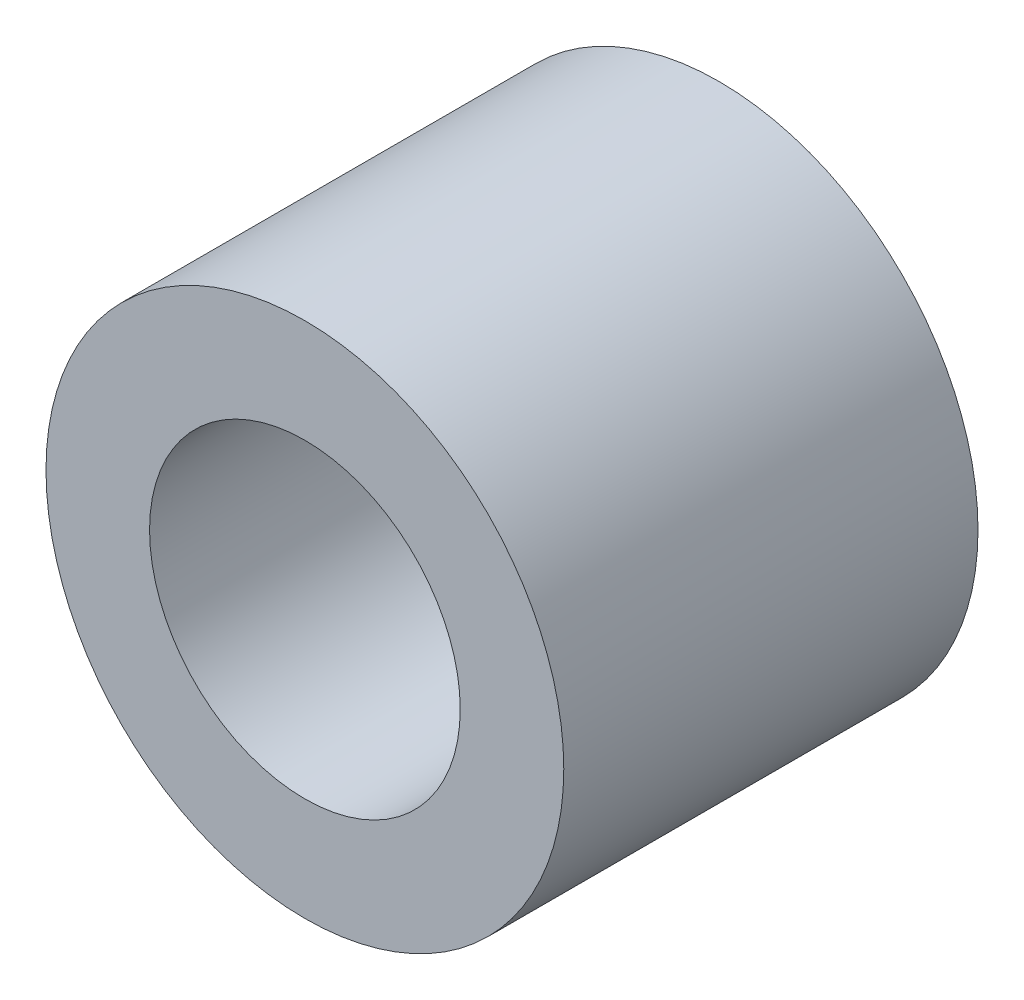
SolidWorks part; units mm, degrees
ref_plane "Płaszczyzna przednia" through (0, 0, 0) normal (0, 0, 1) x (1, 0, 0)
ref_plane "Płaszczyzna górna" through (0, 0, 0) normal (0, 1, 0) x (1, 0, 0)
ref_plane "Płaszczyzna prawa" through (0, 0, 0) normal (1, 0, 0) x (0, 0, -1)
sketch "Sketch1" plane through (0, 0, 0) normal (0, 0, 1) x (1, 0, 0)
  circle A0 centre (0, 0) radius 1.5
  circle A1 centre (0, 0) radius 2.5
  dimension "D1" = 3
  dimension "D2" = 5
extrude "Boss-Extrude1" add sketch "Sketch1" along normal blind 4
